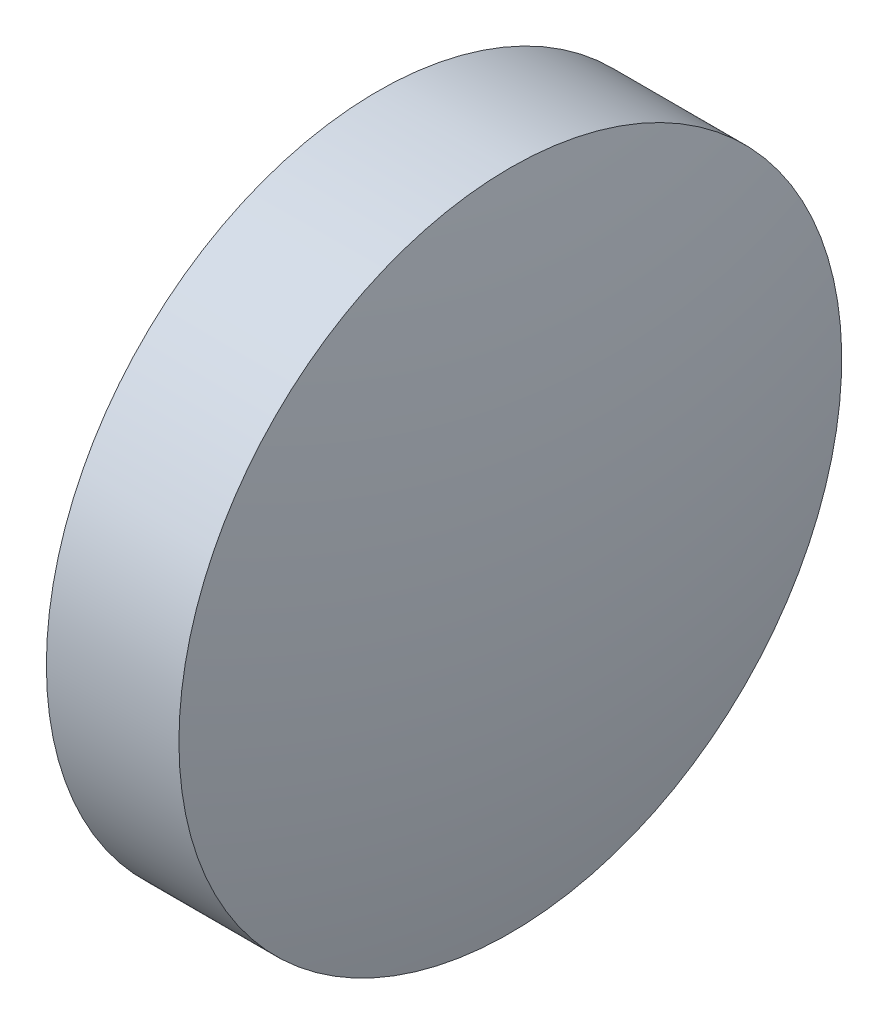
SolidWorks part; units mm, degrees
ref_plane "前视基准面" through (0, 0, 0) normal (0, 0, 1) x (1, 0, 0)
ref_plane "上视基准面" through (0, 0, 0) normal (0, 1, 0) x (1, 0, 0)
ref_plane "右视基准面" through (0, 0, 0) normal (1, 0, 0) x (0, 0, -1)
sketch "草图1" plane through (0, 0, 0) normal (0, 0, 1) x (1, 0, 0)
  line L0 (433.8233, 64.0026) -> (439.475, 64.0026) construction
  line L1 (434.9656, 64.0026) -> (434.9656, 69.0026)
  line L2 (437.5256, 64.0026) -> (434.9656, 64.0026)
  line L5 (434.9656, 69.0026) -> (436.9656, 69.0026)
  arc A0 (437.5256, 64.0026) -> (436.9656, 69.0026) centre (414.9241, 64.0026) ccw
revolve "旋转1" add sketch "草图1" angle 360 about L0
